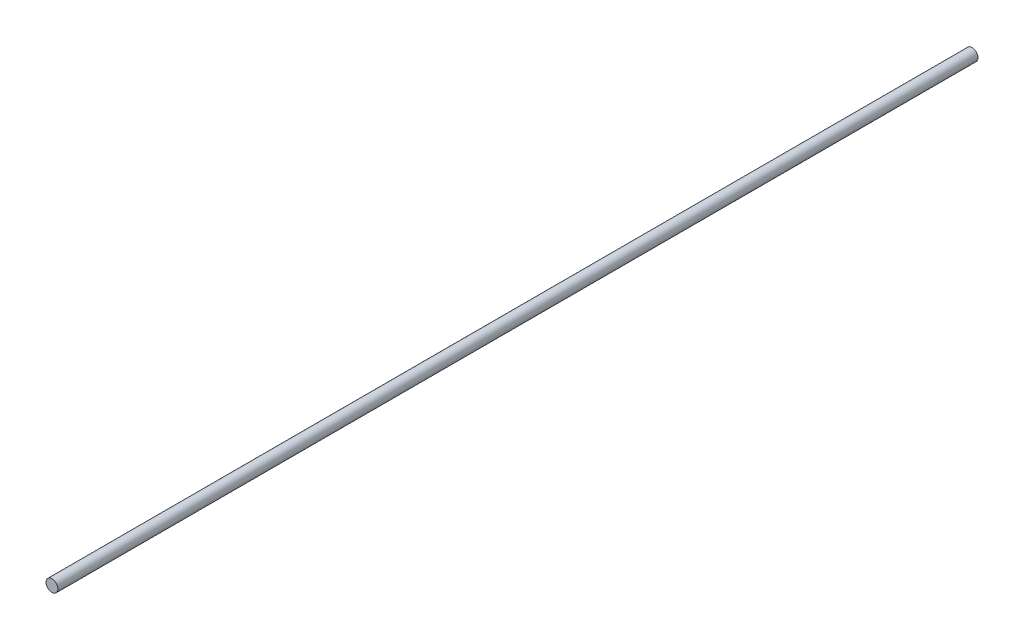
SolidWorks part; units mm, degrees
ref_plane "Plan de face" through (0, 0, 0) normal (0, 0, 1) x (1, 0, 0)
ref_plane "Plan de dessus" through (0, 0, 0) normal (0, 1, 0) x (1, 0, 0)
ref_plane "Plan de droite" through (0, 0, 0) normal (1, 0, 0) x (0, 0, -1)
sketch "Esquisse1" plane through (0, 0, 0) normal (0, 0, 1) x (1, 0, 0)
  circle A0 centre (0, 0) radius 4
  dimension "D1" = 8
extrude "Boss.-Extru.1" add sketch "Esquisse1" along normal blind 620
